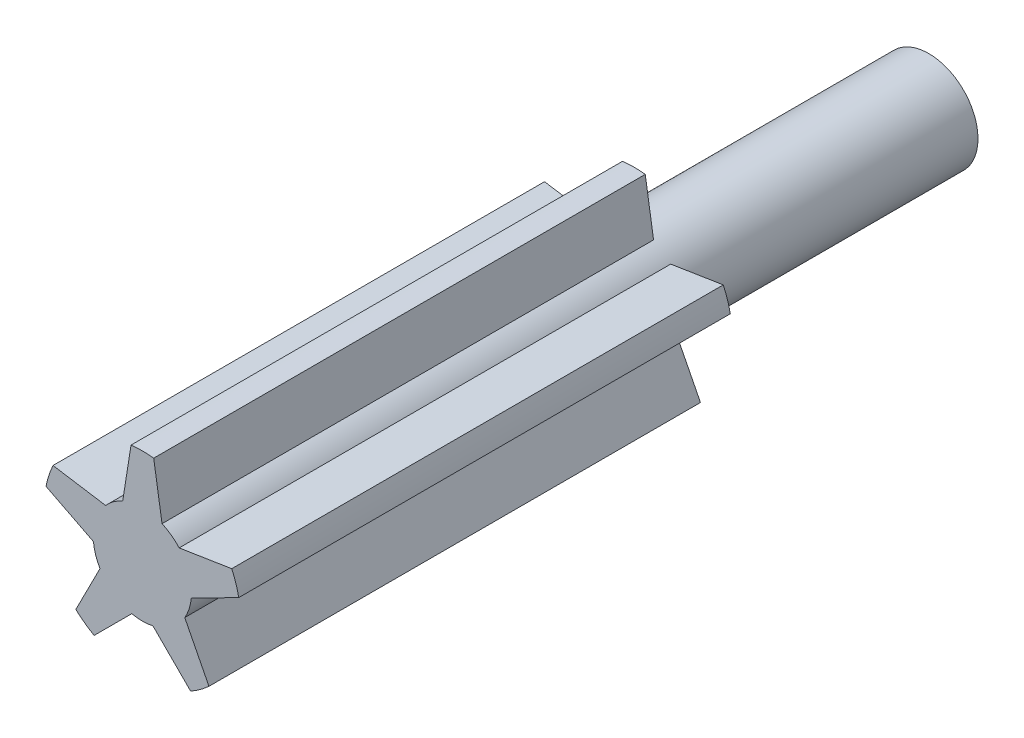
SolidWorks part; units mm, degrees
ref_plane "Front Plane" through (0, 0, 0) normal (0, 0, 1) x (1, 0, 0)
ref_plane "Top Plane" through (0, 0, 0) normal (0, 1, 0) x (1, 0, 0)
ref_plane "Right Plane" through (0, 0, 0) normal (1, 0, 0) x (0, 0, -1)
sketch "Sketch1" plane through (0, 0, 0) normal (0, 0, 1) x (1, 0, 0)
  circle A0 centre (0, 0) radius 10
  dimension "D1" = 20
extrude "Boss-Extrude1" add sketch "Sketch1" along normal mid plane 60
sketch "Sketch2" plane through (0, 0, 30) normal (0, 0, 1) x (1, 0, 0)
  line L0 (0, 0) -> (0, 20.4706) construction
  line L1 (-2.305, 19.8667) -> (-4, 9.1652)
  line L2 (2.305, 19.8667) -> (4, 9.1652)
  line L3 (18.1821, 8.3314) -> (7.4805, 6.6364)
  line L4 (19.6067, 3.9469) -> (9.9526, -0.972)
  line L5 (13.5422, -14.7177) -> (8.6232, -5.0636)
  line L6 (9.8126, -17.4274) -> (2.1511, -9.7659)
  line L7 (-9.8126, -17.4274) -> (-2.1511, -9.7659)
  line L8 (-13.5422, -14.7177) -> (-8.6232, -5.0636)
  line L9 (-19.6067, 3.9469) -> (-9.9526, -0.972)
  line L10 (-18.1821, 8.3314) -> (-7.4805, 6.6364)
  arc A0 (-18.1821, 8.3314) -> (-19.6067, 3.9469) centre (0, 0) ccw
  arc A1 (2.305, 19.8667) -> (-2.305, 19.8667) centre (0, 0) ccw
  circle A2 centre (0, 0) radius 10 construction
  arc A3 (19.6067, 3.9469) -> (18.1821, 8.3314) centre (0, 0) ccw
  arc A4 (9.8126, -17.4274) -> (13.5422, -14.7177) centre (0, 0) ccw
  arc A5 (-13.5422, -14.7177) -> (-9.8126, -17.4274) centre (0, 0) ccw
  point P28 (0, 0)
  dimension "D1" = 40
  dimension "D2" = 9
  dimension "D3" = 4
  dimension "D4" = 5
extrude "Boss-Extrude2" add sketch "Sketch2" along normal blind 100
